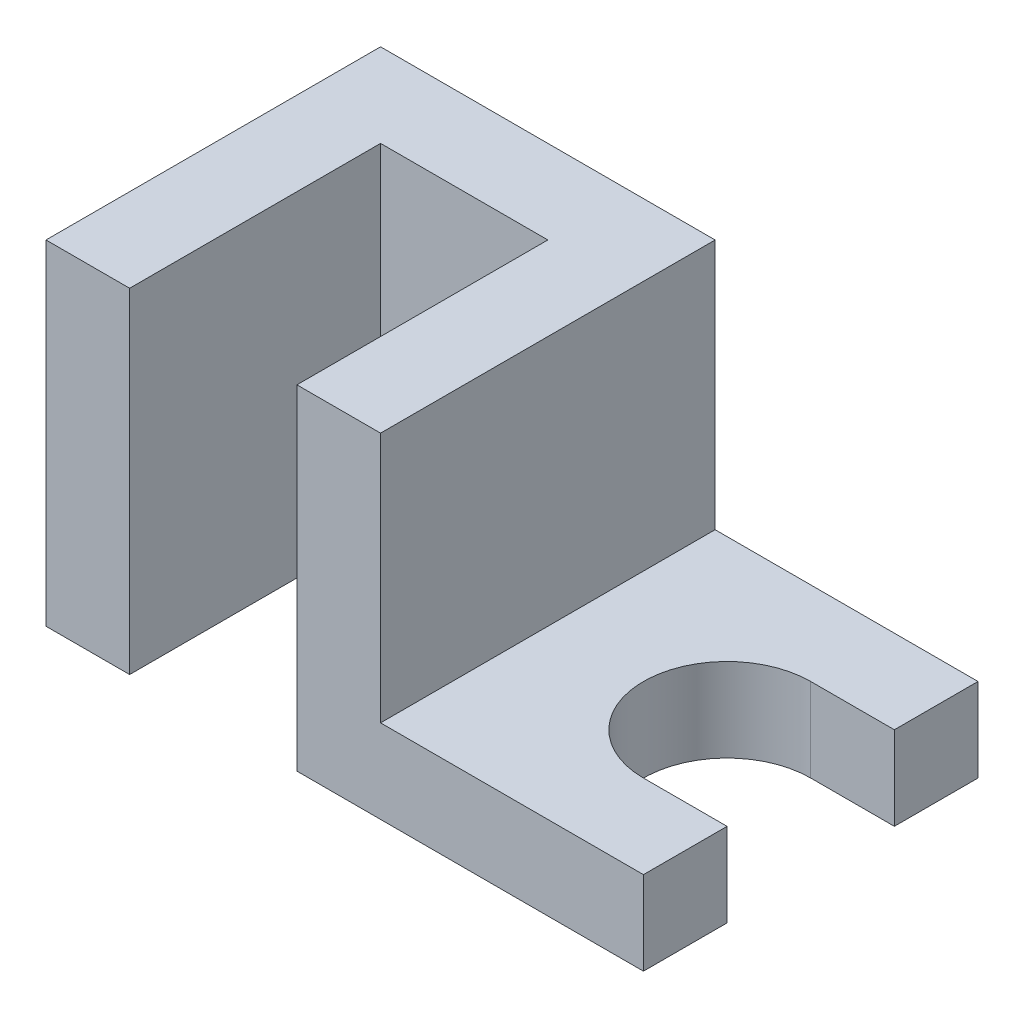
SolidWorks part; units mm, degrees
material "회주철"
ref_plane "정면" through (0, 0, 0) normal (0, 0, 1) x (1, 0, 0)
ref_plane "윗면" through (0, 0, 0) normal (0, 1, 0) x (1, 0, 0)
ref_plane "우측면" through (0, 0, 0) normal (1, 0, 0) x (0, 0, -1)
sketch "스케치1" plane through (0, 0, 0) normal (0, 1, 0) x (1, 0, 0)
  line L0 (7, 0) -> (7, 21)
  line L1 (0, 0) -> (7, 0)
  line L2 (0, 0) -> (0, 28)
  line L3 (0, 28) -> (50, 28)
  line L4 (50, 0) -> (50, 7)
  line L5 (21, 0) -> (21, 21)
  line L6 (43, 7) -> (50, 7)
  line L8 (7, 0) -> (7, 28) construction
  line L9 (50, 21) -> (50, 28)
  line L10 (21, 0) -> (21, 28) construction
  line L11 (21, 0) -> (50, 0)
  line L13 (7, 21) -> (21, 21)
  line L14 (0, 21) -> (50, 21) construction
  line L15 (43, 21) -> (50, 21)
  line L16 (21, 7) -> (50, 7) construction
  arc A0 (43, 21) -> (43, 7) centre (43, 14) ccw
  dimension "D1" = 28
  dimension "D2" = 50
  dimension "D3" = 21
extrude "보스-돌출1" add sketch "스케치1" along normal blind 28
sketch "스케치2" plane through (0, 0, 0) normal (0, 0, 1) x (1, 0, 0)
  line L2 (50, 7) -> (50, 28)
  line L3 (28, 7) -> (50, 7)
  line L5 (28, 28) -> (28, 7)
  line L6 (50, 28) -> (28, 28)
  dimension "D1" = 28
  dimension "D2" = 7
extrude "컷-돌출1" cut sketch "스케치2" against normal through all
